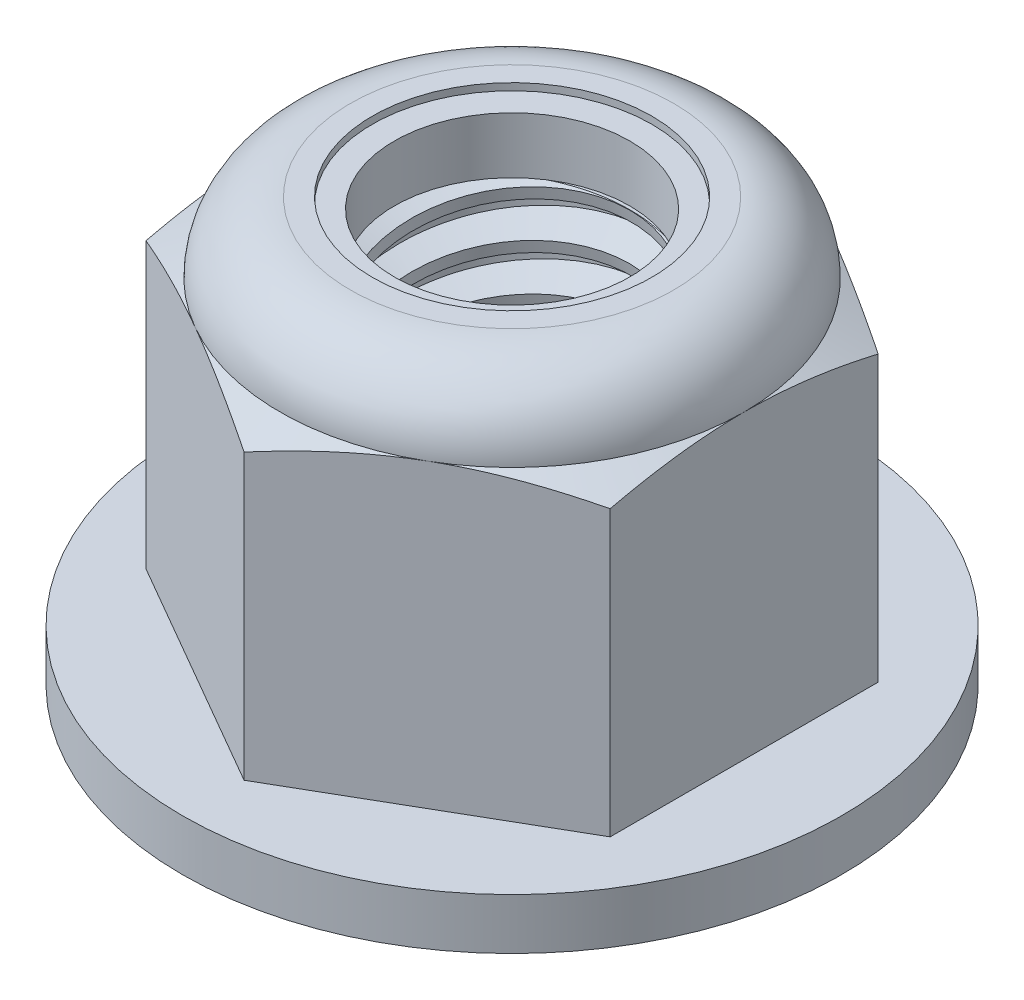
SolidWorks part; units mm, degrees
ref_plane "Front" through (0, 0, 0) normal (0, 0, 1) x (1, 0, 0)
ref_plane "Top" through (0, 0, 0) normal (0, 1, 0) x (1, 0, 0)
ref_plane "Right" through (0, 0, 0) normal (1, 0, 0) x (0, 0, -1)
sketch "Sketch1" plane through (0, 0, 0) normal (0, 1, 0) x (1, 0, 0)
  line L1 (0, 5.7735) -> (-5, 2.8868)
  line L2 (-5, 2.8868) -> (-5, -2.8868)
  line L3 (-5, -2.8868) -> (0, -5.7735)
  line L4 (0, -5.7735) -> (5, -2.8868)
  line L5 (5, -2.8868) -> (5, 2.8868)
  line L6 (5, 2.8868) -> (0, 5.7735)
  circle A0 centre (0, 0) radius 5 construction
  dimension "Hex Flats" = 10
extrude "Extrude1" add sketch "Sketch1" along normal blind 9.1
sketch "Sketch8" plane through (0, 0, 0) normal (1, 0, 0) x (0, 0, -1)
  line L0 (0, 0) -> (7.1, 0)
  line L1 (7.1, 0) -> (7.1, 1.1)
  line L2 (7.1, 1.1) -> (0, 1.1)
  line L3 (0, 1.1) -> (0, 0)
  line L4 (0, 0) -> (0, -1.1) construction
  dimension "Flange Height" = 1.1
  dimension "Flange Dia" = 14.2
revolve "Revolve3" add sketch "Sketch8" angle 360 about L4
sketch "Sketch2" plane through (0, 0, 0) normal (1, 0, 0) x (0, 0, -1)
  line L0 (-3, 0) -> (-3, 9.1) construction
  line L1 (0, 0) -> (3, 0)
  line L2 (0, 0) -> (0, 9.1)
  line L3 (0, 9.1) -> (3, 9.1)
  line L4 (3, 0) -> (3, 9.1)
  line L5 (-2.8868, 9.1) -> (2.8868, 9.1) construction
  line L7 (0, -3) -> (0, 0) construction
  dimension "Thread Dia" = 6
revolve "Revolve1" add sketch "Sketch2" angle 360 about L7
sketch "Sketch3" plane through (0, 0, 0) normal (1, 0, 0) x (0, 0, -1)
  line L0 (3, 9.1) -> (-3, 9.1) construction
  line L1 (-3, 9.1) -> (-3, 8.1) construction
  line L2 (-3, 8.1) -> (3, 9.1) construction
  line L3 (3, 9.1) -> (3.0205, 8.9767) construction
  line L4 (3.0205, 8.9767) -> (3.1644, 8.1136)
  line L5 (3.1644, 8.1136) -> (2.5791, 8.3329)
  line L6 (2.5791, 8.3329) -> (2.538, 8.5795)
  line L7 (2.538, 8.5795) -> (3.0205, 8.9767)
  line L8 (2.5586, 8.4562) -> (3.0925, 8.5452) construction
  line L9 (3, 9.1) -> (3, 8.5297) construction
  line L10 (3, 8.5297) -> (-3, 7.5297) construction
  line L11 (-3, 7.5297) -> (-3, 8.1) construction
  line L12 (-0.1784, 9.1) -> (0.1784, 6.9595) construction
  line L13 (-3, 0) -> (-3, 9.1) construction
  line L14 (0, 9.1) -> (3, 9.1) construction
  line L15 (3, 0) -> (3, 9.1) construction
  point P13 (0, 8.0297)
  dimension "D1" = 0.125
  dimension "D2" = 0.25
  dimension "Thread Pitch" = 1
  dimension "D4" = 60
  dimension "D5" = 1
revolve "Cut-Revolve1" cut sketch "Sketch3" angle 360 about L12
pattern_linear "LPattern1" count 9 spacing 1 along (0, -1, 0) count 2 spacing 1 along (0, 1, 0) of "Cut-Revolve1"
sketch "Sketch4" plane through (0, 0, 0) normal (1, 0, 0) x (0, 0, -1)
  line L0 (0, 9.1) -> (3, 9.1)
  line L1 (3, 9.1) -> (2.538, 8.8846)
  line L2 (2.538, 8.8846) -> (2.538, 0.2154)
  line L3 (2.538, 0.2154) -> (3, 0)
  line L4 (3, 0) -> (0, 0)
  line L5 (0, 0) -> (0, 9.1)
  line L6 (3, 0) -> (3, 9.1) construction
  line L7 (0, 9.1) -> (3, 9.1) construction
  line L8 (0, 0) -> (3, 0) construction
  line L9 (0, 0) -> (0, 9.1) construction
  line L10 (0, 9.1) -> (0, 9.6097) construction
  dimension "D1" = 25
revolve "Cut-Revolve2" cut sketch "Sketch4" angle 360 about L10
combine bodies "Combine1" operation type subtract main body 112 bodies to subtract 111
sketch "Sketch5" plane through (0, 0, 0) normal (1, 0, 0) x (0, 0, -1)
  line L0 (7.1, 1.1) -> (0, 1.1) construction
  line L1 (0, 0) -> (7.1, 0) construction
  line L2 (5.7735, 1.1) -> (5.7735, 7.2226)
  line L3 (5.7735, 7.2226) -> (5, 7.5833)
  line L4 (3.4833, 9.1) -> (3.4833, 10.37)
  line L5 (3.4833, 10.37) -> (7.0435, 10.37)
  line L6 (7.0435, 10.37) -> (7.0435, 1.1)
  line L9 (5, 7.5833) -> (5, 0) construction
  line L13 (5.7735, 1.1) -> (7.0435, 1.1)
  line L15 (0, 0) -> (0, 10.37) construction
  line L20 (0, 10.37) -> (3.4833, 10.37) construction
  line L22 (0, 9.1) -> (3, 9.1) construction
  arc A0 (5, 7.5833) -> (3.4833, 9.1) centre (3.4833, 7.5833) ccw
  dimension "D1" = 1.27
  dimension "D2" = 115
  dimension "D3" = 9.1
  dimension "D4" = 1.5167
revolve "Cut-Revolve3" cut sketch "Sketch5" angle 360 about L15
sketch "Sketch6" plane through (0, 0, 0) normal (1, 0, 0) x (0, 0, -1)
  line L0 (0, 7.5833) -> (4.8476, 7.5833)
  line L1 (3.4833, 8.9476) -> (3.0107, 8.9476)
  line L2 (0, 10.37) -> (0, 7.5833)
  line L3 (3.0107, 10.37) -> (0, 10.37)
  line L4 (0, 10.37) -> (3.4833, 10.37) construction
  line L5 (0, 0) -> (0, 10.37) construction
  line L6 (0, 10.37) -> (0, 44.323) construction
  line L7 (3.0107, 8.9476) -> (3.0107, 10.37)
  line L8 (3.4833, 9.1) -> (3.4833, 8.9476) construction
  line L9 (3.0107, 8.9476) -> (2.538, 8.9476) construction
  line L10 (2.538, 8.9476) -> (2.538, 8.8846) construction
  arc A0 (4.8476, 7.5833) -> (3.4833, 8.9476) centre (3.4833, 7.5833) ccw
  arc A1 (5, 7.5833) -> (3.4833, 9.1) centre (3.4833, 7.5833) ccw construction
  dimension "D1" = 0.1524
revolve "Cut-Revolve4" cut sketch "Sketch6" angle 360 about L6
sketch "Sketch7" plane through (0, 0, 0) normal (1, 0, 0) x (0, 0, -1)
  line L0 (2.538, 7.6595) -> (4.7691, 7.6595)
  line L1 (3.4833, 8.8714) -> (2.538, 8.8714)
  line L2 (2.538, 8.8714) -> (2.538, 7.6595)
  line L3 (2.538, 7.6595) -> (0, 7.6595) construction
  line L4 (0, 7.6595) -> (0, 8.8714) construction
  line L5 (0, 8.8714) -> (2.538, 8.8714) construction
  line L6 (2.538, 7.6595) -> (2.538, 7.5833) construction
  line L7 (0, 7.5833) -> (4.8476, 7.5833) construction
  line L8 (3.4833, 8.8714) -> (3.4833, 8.9476) construction
  arc A0 (4.7691, 7.6595) -> (3.4833, 8.8714) centre (3.4833, 7.5833) ccw
  arc A2 (4.8476, 7.5833) -> (3.4833, 8.9476) centre (3.4833, 7.5833) ccw construction
  dimension "D1" = 0.0762
revolve "Revolve2" add sketch "Sketch7" angle 360 about L4
equation "\"D1@Sketch3\"=\"Thread Pitch@Sketch3\"/8"
equation "\"D2@Sketch3\"=\"Thread Pitch@Sketch3\"/4"
equation "\"D5@Sketch3\"=\"Thread Pitch@Sketch3\""
equation "\"D4@LPattern1\"=\"Thread Pitch@Sketch3\""
equation "\"D3@LPattern1\"=\"Thread Pitch@Sketch3\""
equation "\"D1@LPattern1\"=\"Height@Extrude1\"/\"Thread Pitch@Sketch3\""
equation "\"D4@Sketch5\"=\"Height@Extrude1\"/6"
